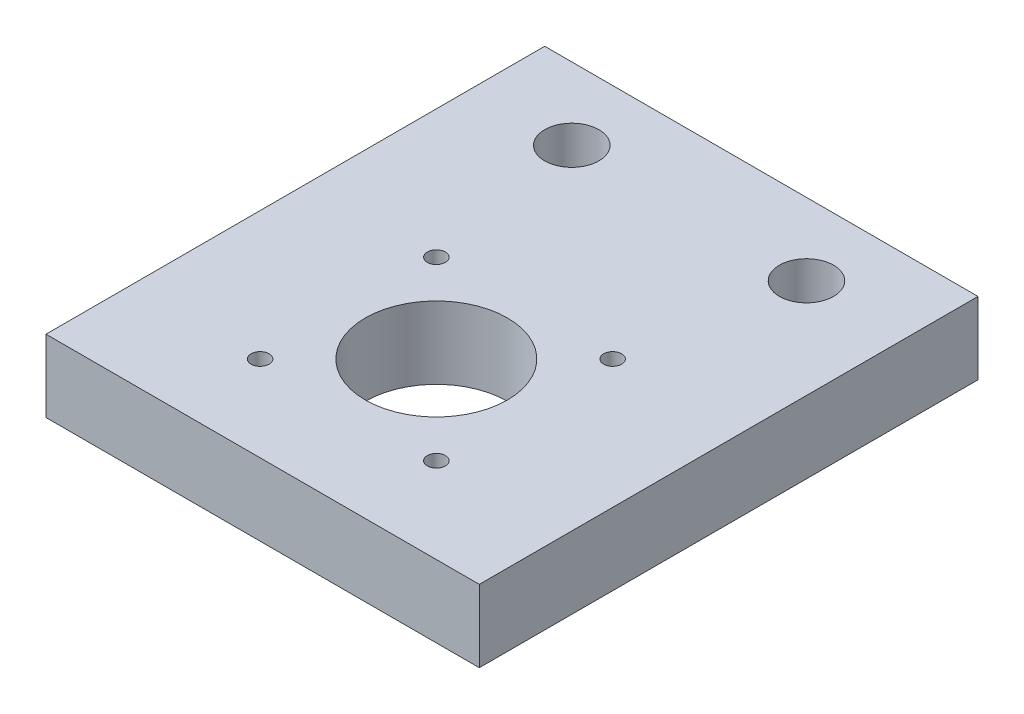
SolidWorks part; units mm, degrees
ref_plane "Front Plane" through (0, 0, 0) normal (0, 0, 1) x (1, 0, 0)
ref_plane "Top Plane" through (0, 0, 0) normal (0, 1, 0) x (1, 0, 0)
ref_plane "Right Plane" through (0, 0, 0) normal (1, 0, 0) x (0, 0, -1)
sketch "Sketch1" plane through (0, 0, 0) normal (0, 1, 0) x (1, 0, 0)
  line L0 (-17.4625, 12.7) -> (58.7375, 12.7)
  line L1 (58.7375, 12.7) -> (58.7375, -75)
  line L2 (58.7375, -75) -> (-17.4625, -75)
  line L3 (-17.4625, -75) -> (-17.4625, 12.7)
  circle A0 centre (0, 0) radius 4.7625
  circle A1 centre (41.275, 0) radius 4.7625
extrude "Boss-Extrude1" add sketch "Sketch1" along normal blind 12.7
sketch "Sketch2" plane through (0, 12.7, 0) normal (0, 1, 0) x (1, 0, 0)
  circle A0 centre (20.6375, -44.45) radius 12.5
  circle A1 centre (36.1375, -28.95) radius 1.5875
  circle A2 centre (5.1375, -28.95) radius 1.5875
  circle A3 centre (36.1375, -59.95) radius 1.5875
  circle A4 centre (5.1375, -59.95) radius 1.5875
  dimension "D1" = 2
  dimension "D2" = 2
extrude "Cut-Extrude1" cut sketch "Sketch2" against normal blind 12.7
